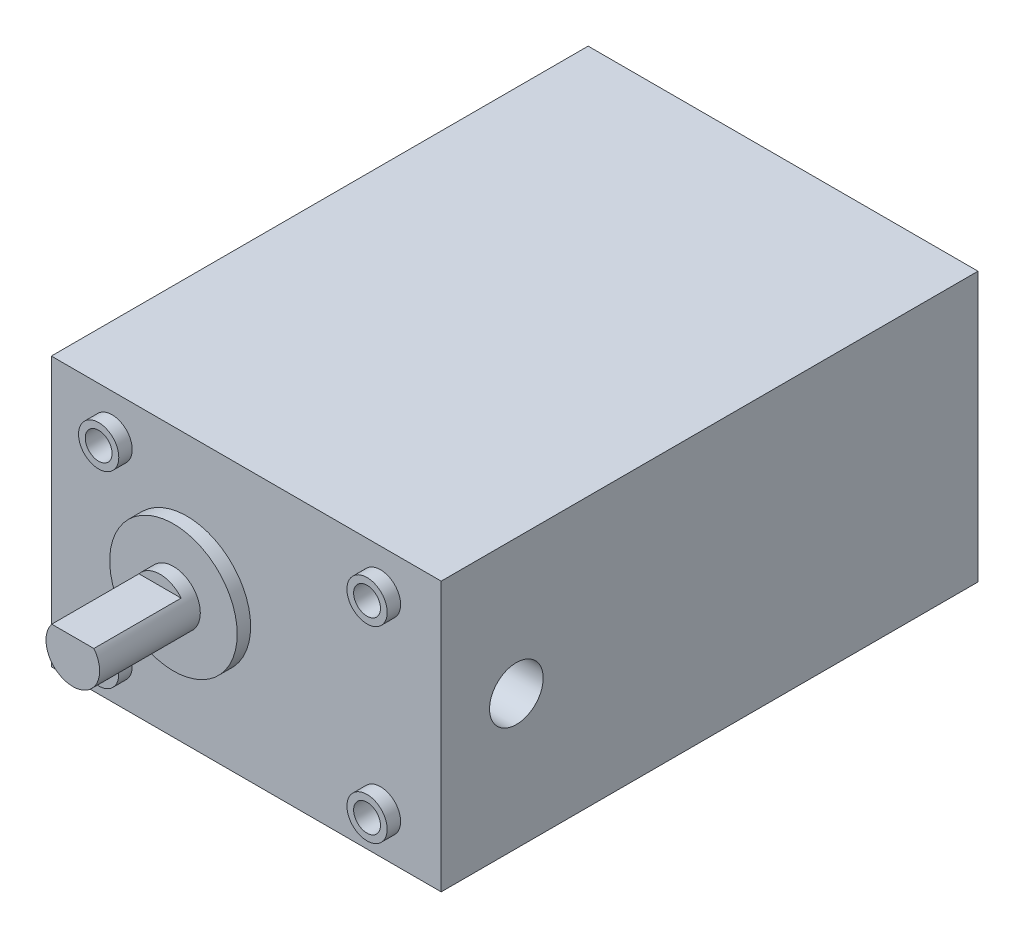
SolidWorks part; units mm, degrees
ref_plane "Front Plane" through (0, 0, 0) normal (0, 0, 1) x (1, 0, 0)
ref_plane "Top Plane" through (0, 0, 0) normal (0, 1, 0) x (1, 0, 0)
ref_plane "Right Plane" through (0, 0, 0) normal (1, 0, 0) x (0, 0, -1)
sketch "Sketch1" plane through (0, 0, 0) normal (0, 0, 1) x (1, 0, 0)
  line L1 (0, 0) -> (58.1, 0)
  line L2 (0, 0) -> (0, 40.11)
  line L3 (0, 40.11) -> (58.1, 40.11)
  line L4 (58.1, 0) -> (58.1, 40.11)
  dimension "D1" = 40.11
  dimension "D2" = 58.1
extrude "Boss-Extrude1" add sketch "Sketch1" along normal blind 80
sketch "Sketch2" plane through (0, 0, 80) normal (0, 0, 1) x (1, 0, 0)
  line L0 (58.1, 0) -> (58.1, 40.11) construction
  circle A0 centre (20.2, 20.055) radius 9.5
  dimension "D1" = 19
  dimension "D2" = 37.9
extrude "Boss-Extrude2" add sketch "Sketch2" along normal blind 2
sketch "Sketch3" plane through (0, 0, 82) normal (0, 0, 1) x (1, 0, 0)
  circle A0 centre (20.2, 20.055) radius 4
  dimension "D1" = 8
extrude "Boss-Extrude3" add sketch "Sketch3" along normal blind 15
sketch "Sketch4" plane through (0, 0, 97) normal (0, 0, 1) x (1, 0, 0)
  line L0 (17.0616, 22.535) -> (23.3384, 22.535)
  line L1 (23.3384, 22.535) -> (23.3384, 24.5338)
  line L2 (23.3384, 24.5338) -> (17.0616, 24.5338)
  line L3 (17.0616, 24.5338) -> (17.0616, 22.535)
  circle A0 centre (20.2, 20.055) radius 4 construction
extrude "Cut-Extrude1" cut sketch "Sketch4" against normal blind 13
sketch "Sketch5" plane through (0, 0, 80) normal (0, 0, 1) x (1, 0, 0)
  line L0 (29.05, 40.11) -> (29.05, 0) construction
  line L1 (58.1, 40.11) -> (0, 40.11) construction
  line L2 (0, 0) -> (58.1, 0) construction
  line L3 (0, 20.055) -> (58.1, 20.055) construction
  line L4 (0, 40.11) -> (0, 0) construction
  line L5 (58.1, 0) -> (58.1, 40.11) construction
  circle A0 centre (9.05, 34.055) radius 3
  circle A2 centre (49.05, 34.055) radius 3
  circle A3 centre (49.05, 6.055) radius 3
  circle A4 centre (9.05, 6.055) radius 3
  dimension "D3" = 6
  dimension "D1" = 20
  dimension "D2" = 14
extrude "Boss-Extrude4" add sketch "Sketch5" along normal blind 2
sketch "Sketch6" plane through (0, 0, 82) normal (0, 0, 1) x (1, 0, 0)
  circle A0 centre (9.05, 34.055) radius 2
  circle A1 centre (49.05, 34.055) radius 2
  circle A2 centre (49.05, 6.055) radius 2
  circle A3 centre (9.05, 6.055) radius 2
  dimension "D1" = 4
extrude "Cut-Extrude2" cut sketch "Sketch6" against normal blind 8
sketch "Sketch7" plane through (58.1, 0, 0) normal (1, 0, 0) x (0, 0, -1)
  line L0 (-80, 0) -> (0, 0) construction
  line L1 (-80, 0) -> (-80, 40.11) construction
  circle A0 centre (-68.7979, 20) radius 4
  dimension "D1" = 8
  dimension "D2" = 20
  dimension "D3" = 11.2021
extrude "Cut-Extrude3" cut sketch "Sketch7" against normal blind 25.4
